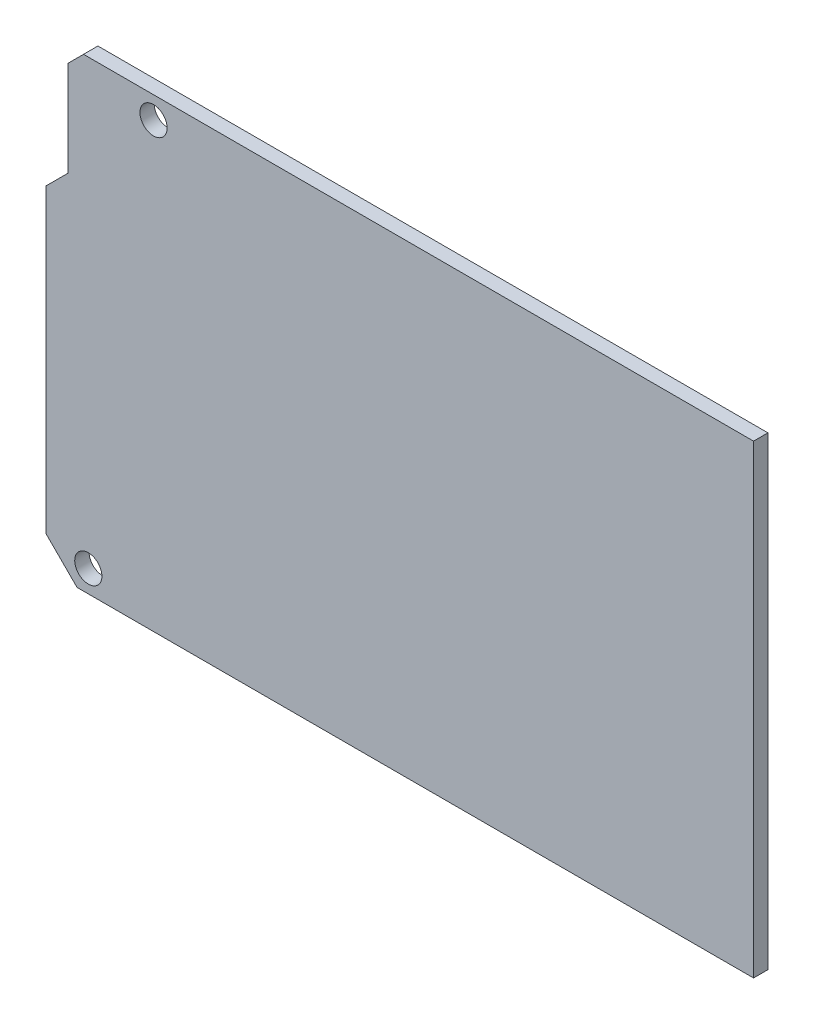
SolidWorks part; units mm, degrees
ref_plane "Front Plane" through (0, 0, 0) normal (0, 0, 1) x (1, 0, 0)
ref_plane "Top Plane" through (0, 0, 0) normal (0, 1, 0) x (1, 0, 0)
ref_plane "Right Plane" through (0, 0, 0) normal (1, 0, 0) x (0, 0, -1)
sketch "Sketch1" plane through (0, 0, 0) normal (0, 0, 1) x (1, 0, 0)
  line L1 (-50.8, 26.7081) -> (50.8, 26.7081)
  line L2 (-50.8, 26.7081) -> (-50.8, -26.7081)
  line L3 (-50.8, -26.7081) -> (50.8, -26.7081)
  line L4 (50.8, 26.7081) -> (50.8, -26.7081)
  line L5 (-50.8, 26.7081) -> (50.8, -26.7081) construction
  line L6 (-50.8, -26.7081) -> (50.8, 26.7081) construction
  point P0 (0, 0)
  dimension "D1" = 101.6
  dimension "D2" = 53.4162
extrude "Boss-Extrude1" add sketch "Sketch1" along normal blind 1.651
chamfer "Chamfer3" distance 3.556 angle 45 1 edges at (-50.8, -26.7081, 0.8255)
sketch "Sketch13" plane through (0, 0, 0) normal (0, 0, -1) x (-1, 0, 0)
  line L1 (50.8, 26.7081) -> (50.8, -23.1521) construction
  line L2 (-50.8, 26.7081) -> (50.8, 26.7081) construction
  line L3 (48.26, 24.9447) -> (48.26, 14.0081)
  line L4 (50.8, 11.4681) -> (48.26, 14.0081)
  line L5 (48.26, 24.9447) -> (46.4966, 26.7081)
  line L6 (46.4966, 26.7081) -> (50.8, 26.7081)
  line L7 (50.8, 26.7081) -> (50.8, 11.4681)
  dimension "D2" = 2.54
extrude "Cut-Extrude4" cut sketch "Sketch13" against normal up to next
sketch "Sketch22" plane through (0, 0, 0) normal (0, 0, -1) x (-1, 0, 0)
  line L1 (47.244, -26.7081) -> (-50.8, -26.7081) construction
  line L3 (-50.8, 26.7081) -> (46.4966, 26.7081) construction
  circle A0 centre (38.4556, 24.1681) radius 1.5621
  circle A3 centre (45.9486, -24.1681) radius 1.5621
  dimension "D1" = 3.1242
  dimension "D4" = 2.54
  dimension "D7" = 2.54
extrude "Cut-Extrude5" cut sketch "Sketch22" against normal up to next
sketch "Esquisse1" plane through (50.8, 0, 0) normal (1, 0, 0) x (0, 0, -1)
  line L1 (0, 26.7081) -> (-1.651, 26.7081)
  line L2 (0, 26.7081) -> (0, -26.7081)
  line L3 (0, -26.7081) -> (-1.651, -26.7081)
  line L4 (-1.651, 26.7081) -> (-1.651, -26.7081)
extrude "Enlèv. mat.-Extru.1" cut sketch "Esquisse1" against normal blind 20.32
